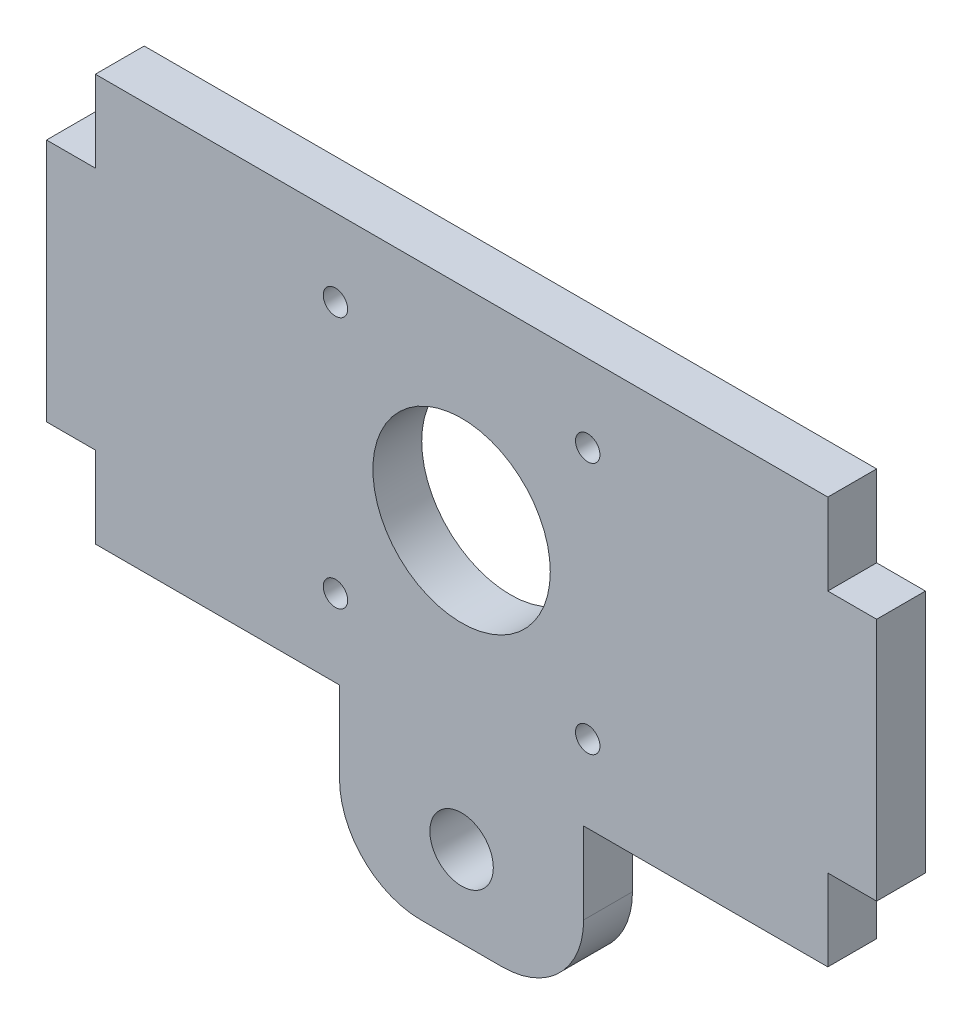
SolidWorks part; units mm, degrees
ref_plane "Alzado" through (0, 0, 0) normal (0, 0, 1) x (1, 0, 0)
ref_plane "Planta" through (0, 0, 0) normal (0, 1, 0) x (1, 0, 0)
ref_plane "Vista lateral" through (0, 0, 0) normal (1, 0, 0) x (0, 0, -1)
sketch "Croquis1" plane through (0, 0, 0) normal (0, 0, 1) x (1, 0, 0)
  line L0 (15, -25) -> (45, -25)
  line L1 (-45, -25) -> (-15, -25)
  line L2 (-45, -25) -> (-45, 25)
  line L3 (-45, 25) -> (45, 25)
  line L4 (45, -25) -> (45, 25)
  line L5 (-45, -25) -> (45, 25) construction
  line L6 (-45, 25) -> (45, -25) construction
  line L7 (-15, -45) -> (15, -45)
  line L8 (-15, -45) -> (-15, -25)
  line L10 (15, -45) -> (15, -25)
  line L11 (-15, -45) -> (15, -25) construction
  line L12 (-15, -25) -> (15, -45) construction
  point P0 (0, 0)
  point P6 (0, -35)
  dimension "D1" = 90
  dimension "D2" = 50
  dimension "D3" = 20
  dimension "D4" = 30
extrude "Saliente-Extruir1" add sketch "Croquis1" along normal blind 6
sketch "Croquis2" plane through (-45, 0, 0) normal (-1, 0, 0) x (0, 0, 1)
  line L0 (0, 25) -> (0, -25) construction
  line L1 (0, 15) -> (6, 15)
  line L2 (0, 15) -> (0, -15)
  line L3 (0, -15) -> (6, -15)
  line L4 (6, 15) -> (6, -15)
  line L5 (6, 25) -> (6, -25) construction
  point P8 (0, 0)
  dimension "D1" = 30
extrude "Saliente-Extruir2" add sketch "Croquis2" along normal blind 6 and the other way blind 96
sketch "Croquis3" plane through (0, 0, 6) normal (0, 0, 1) x (1, 0, 0)
  line L0 (-15, -25) -> (-15, -45) construction
  line L1 (-15.5, -15.5) -> (15.5, -15.5) construction
  line L2 (-15.5, -15.5) -> (-15.5, 15.5) construction
  line L3 (-15.5, 15.5) -> (15.5, 15.5) construction
  line L4 (15.5, -15.5) -> (15.5, 15.5) construction
  line L5 (-15.5, -15.5) -> (15.5, 15.5) construction
  line L6 (-15.5, 15.5) -> (15.5, -15.5) construction
  circle A0 centre (-15.5, 15.5) radius 1.5
  circle A1 centre (15.5, 15.5) radius 1.5
  circle A2 centre (15.5, -15.5) radius 1.5
  circle A3 centre (-15.5, -15.5) radius 1.5
  circle A4 centre (0, 0) radius 10.9
  circle A5 centre (0, -35) radius 3.9
  point P0 (0, 0)
  point P17 (-15, -35)
  dimension "D3" = 3
  dimension "D4" = 3
  dimension "D5" = 3
  dimension "D6" = 3
  dimension "D7" = 21.8
  dimension "D8" = 7.8
  dimension "D1" = 31
  dimension "D2" = 31
extrude "Cortar-Extruir1" cut sketch "Croquis3" against normal up to next
fillet "Redondeo2" radius 10 2 edges at (15, -45, 3) (-15, -45, 3)
